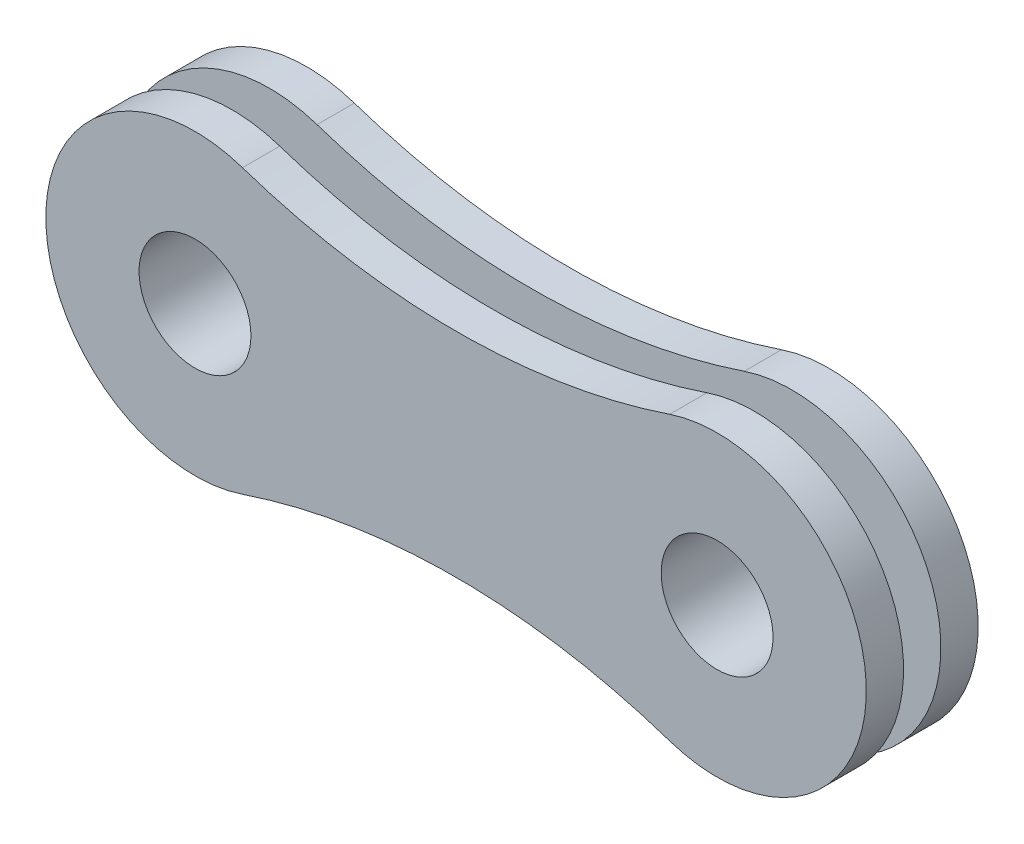
SolidWorks part; units mm, degrees
ref_plane "Front Plane" through (0, 0, 0) normal (0, 0, 1) x (1, 0, 0)
ref_plane "Top Plane" through (0, 0, 0) normal (0, 1, 0) x (1, 0, 0)
ref_plane "Right Plane" through (0, 0, 0) normal (1, 0, 0) x (0, 0, -1)
sketch "Sketch1" plane through (0, 0, 0) normal (0, 0, 1) x (1, 0, 0)
  line L0 (74.6129, 0) -> (-64.3109, 0) construction
  circle A0 centre (-7, 0) radius 1.5
  circle A1 centre (-7, 0) radius 4
  circle A2 centre (7, 0) radius 1.5
  circle A3 centre (7, 0) radius 4
  arc A4 (-5.7273, 3.7921) -> (5.7273, 3.7921) centre (0, 20.8567) ccw
  arc A5 (5.7273, -3.7921) -> (-5.7273, -3.7921) centre (0, -20.8567) ccw
  dimension "D1" = 8
  dimension "D2" = 3
  dimension "D5" = 18
  dimension "D6" = 18
  dimension "D3" = 7
  dimension "D4" = 7
extrude "Boss-Extrude1" add sketch "Sketch1" along normal blind 1 contours L0 A3 A4 A1 | L0 A1 A0 | L0 A3 A2 | A3 L0 A2 | A3 L0 A1 A5 | A1 L0 A0
sketch "Sketch2" plane through (0, 0, 1) normal (0, 0, 1) x (1, 0, 0)
  circle A0 centre (-7, 0) radius 2
  circle A1 centre (7, 0) radius 2
  circle A2 centre (-7, 0) radius 1.5
  circle A3 centre (7, 0) radius 1.5
  circle A4 centre (7, 0) radius 1.5 construction
  circle A5 centre (-7, 0) radius 1.5 construction
  dimension "D1" = 4
extrude "Boss-Extrude2" add sketch "Sketch2" along normal blind 2
ref_plane "Plane1" through (0, 0, 1.5) normal (0, 0, 1) x (1, 0, 0)
mirror "Mirror1" about plane through (0, 0, 1.5) normal (0, 0, 1) of "Boss-Extrude1"
